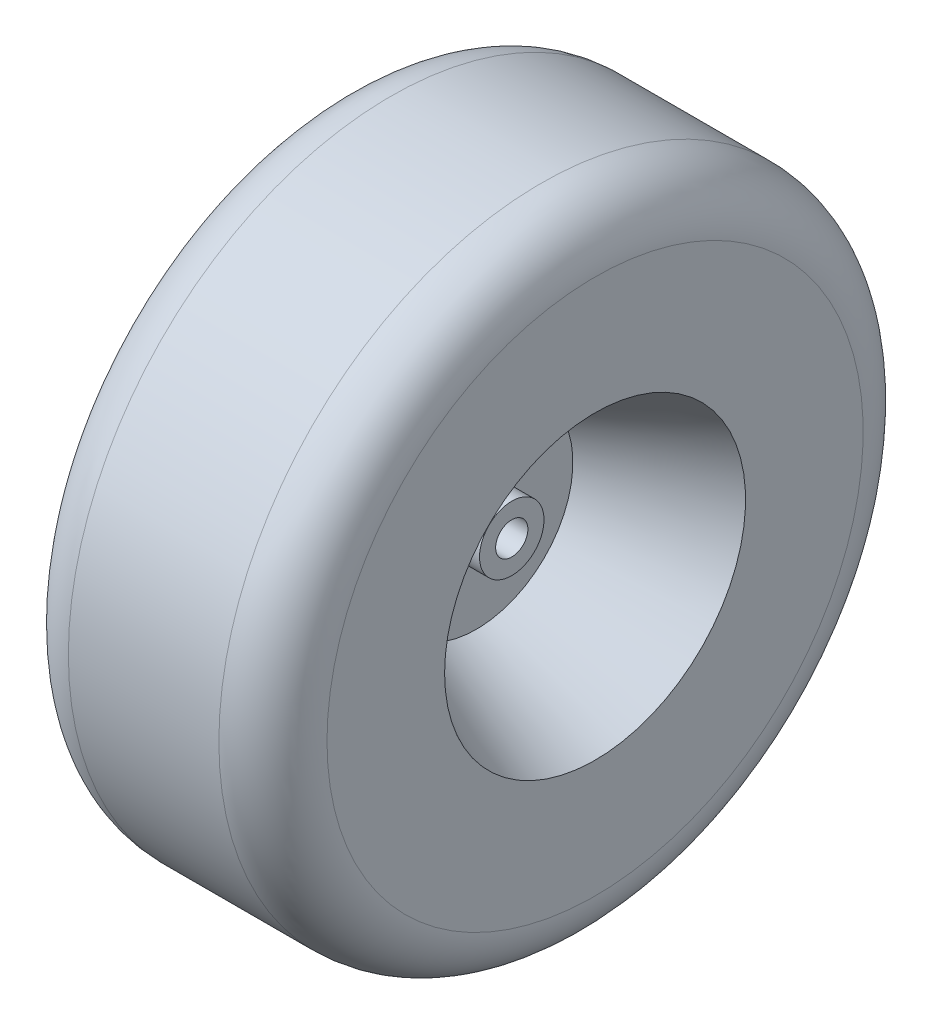
SolidWorks part; units mm, degrees
ref_plane "Front Plane" through (0, 0, 0) normal (0, 0, 1) x (1, 0, 0)
ref_plane "Top Plane" through (0, 0, 0) normal (0, 1, 0) x (1, 0, 0)
ref_plane "Right Plane" through (0, 0, 0) normal (1, 0, 0) x (0, 0, -1)
sketch "Sketch1" plane through (0, 0, 0) normal (0, 0, 1) x (1, 0, 0)
  line L0 (0, 0) -> (0, 190.5) construction
  line L1 (-76.2, 190.5) -> (76.2, 190.5) construction
  line L2 (76.2, 190.5) -> (76.2, 88.9) construction
  line L3 (-76.2, 0) -> (76.2, 0) construction
  line L4 (0, 0) -> (0, 9.525) construction
  line L5 (-26.9875, 9.525) -> (26.9875, 9.525)
  line L6 (76.2, 88.9) -> (76.2, 0) construction
  line L7 (26.9875, 9.525) -> (26.9875, 19.05)
  line L8 (26.9875, 19.05) -> (6.1126, 19.05)
  line L9 (6.1126, 19.05) -> (6.1126, 56.9746)
  line L10 (6.1126, 56.9746) -> (76.2, 88.9)
  line L11 (-44.45, 190.5) -> (44.45, 190.5)
  line L12 (76.2, 88.9) -> (76.2, 158.373)
  line L13 (-76.2, 88.9) -> (-76.2, 0) construction
  line L14 (-76.2, 190.5) -> (-76.2, 88.9) construction
  line L15 (-76.2, 88.9) -> (-76.2, 158.373)
  line L16 (-6.1126, 56.9746) -> (-76.2, 88.9)
  line L17 (-6.1126, 19.05) -> (-6.1126, 56.9746)
  line L18 (-26.9875, 19.05) -> (-6.1126, 19.05)
  line L19 (-26.9875, 9.525) -> (-26.9875, 19.05)
  arc A0 (44.45, 190.5) -> (76.2, 158.373) centre (44.073, 158.3752) cw
  arc A1 (-44.45, 190.5) -> (-76.2, 158.373) centre (-44.073, 158.3752) ccw
  point P11 (0, 9.525)
  dimension "D1" = 190.5
  dimension "D2" = 76.2
  dimension "D3" = 101.6
  dimension "D4" = 9.525
  dimension "D5" = 49.2125
  dimension "D6" = 9.525
  dimension "D7" = 44.45
revolve "Revolve1" add sketch "Sketch1" angle 360 about L3
